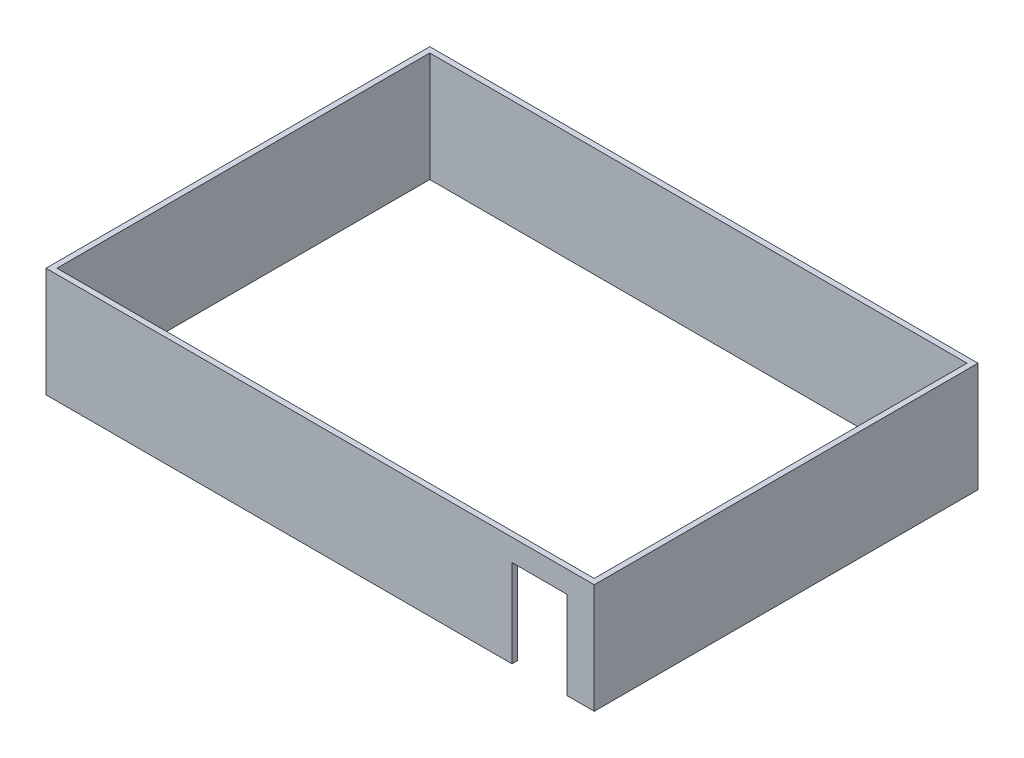
SolidWorks part; units mm, degrees
ref_plane "Front Plane" through (0, 0, 0) normal (0, 0, 1) x (1, 0, 0)
ref_plane "Top Plane" through (0, 0, 0) normal (0, 1, 0) x (1, 0, 0)
ref_plane "Right Plane" through (0, 0, 0) normal (1, 0, 0) x (0, 0, -1)
sketch "Sketch1" plane through (0, 0, 0) normal (0, 1, 0) x (1, 0, 0)
  line L1 (-500, -350) -> (500, -350)
  line L2 (-500, -350) -> (-500, 350)
  line L3 (-500, 350) -> (500, 350)
  line L4 (500, -350) -> (500, 350)
  line L5 (-500, -350) -> (500, 350) construction
  line L6 (-500, 350) -> (500, -350) construction
  line L7 (-490, 340) -> (490, 340)
  line L8 (-490, 340) -> (-490, -340)
  line L9 (-490, -340) -> (490, -340)
  line L10 (490, 340) -> (490, -340)
  line L11 (-490, 340) -> (490, -340) construction
  line L12 (-490, -340) -> (490, 340) construction
  point P0 (0, 0)
  point P6 (0, 0)
  dimension "D1" = 1000
  dimension "D2" = 700
  dimension "D3" = 10
  dimension "D4" = 10
extrude "Boss-Extrude1" add sketch "Sketch1" along normal blind 200
sketch "Sketch2" plane through (0, 0, 350) normal (0, 0, 1) x (1, 0, 0)
  line L0 (-500, 0) -> (500, 0) construction
  line L1 (450, 0) -> (350, 0)
  line L2 (450, 0) -> (450, 160)
  line L3 (450, 160) -> (350, 160)
  line L4 (350, 0) -> (350, 160)
  line L5 (500, 200) -> (500, 0) construction
  dimension "D1" = 50
  dimension "D2" = 100
  dimension "D3" = 160
extrude "Cut-Extrude1" cut sketch "Sketch2" against normal blind 200
